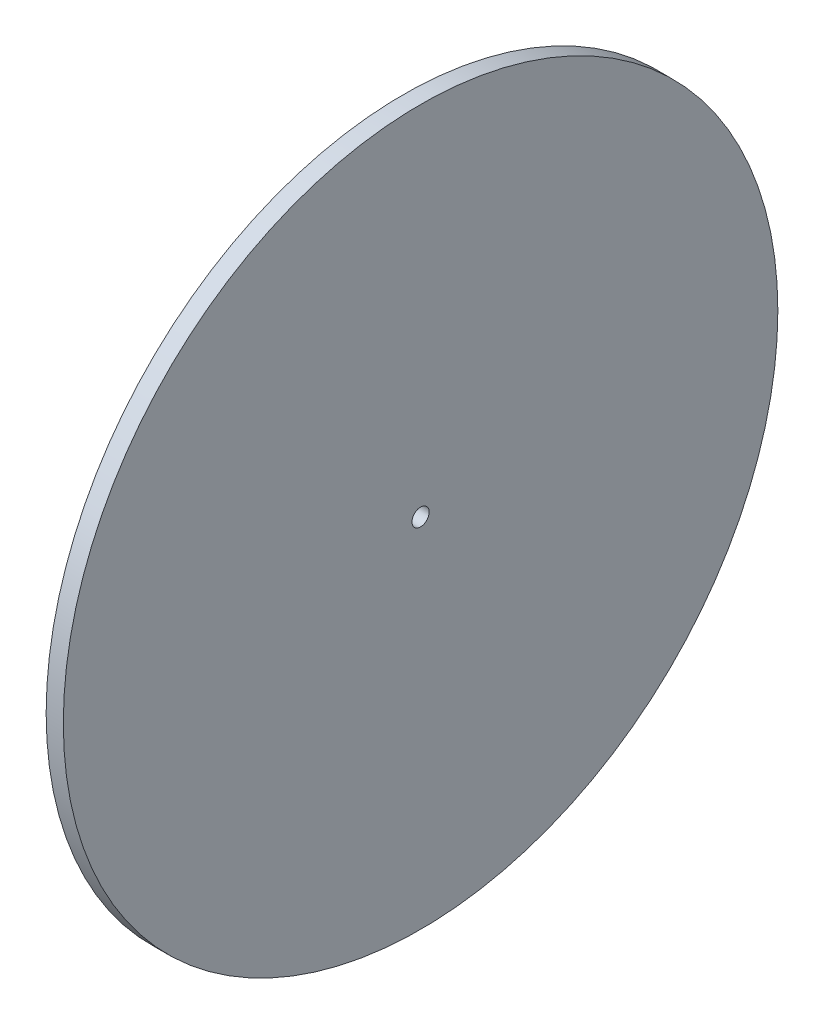
SolidWorks part; units mm, degrees
material "1023 Carbon Steel Sheet (SS)"
ref_plane "Front Plane" through (0, 0, 0) normal (0, 0, 1) x (1, 0, 0)
ref_plane "Top Plane" through (0, 0, 0) normal (0, 1, 0) x (1, 0, 0)
ref_plane "Right Plane" through (0, 0, 0) normal (1, 0, 0) x (0, 0, -1)
sketch "Sketch1" plane through (0, 0, 0) normal (1, 0, 0) x (0, 0, -1)
  circle A0 centre (0, 0) radius 62.5
  dimension "D1" = 125
extrude "Boss-Extrude1" add sketch "Sketch1" along normal blind 3
sketch "Sketch2" plane through (0, 0, 0) normal (-1, 0, 0) x (0, 0, 1)
  circle A0 centre (0, 0) radius 1.5
extrude "Cut-Extrude1" cut sketch "Sketch2" against normal through all
